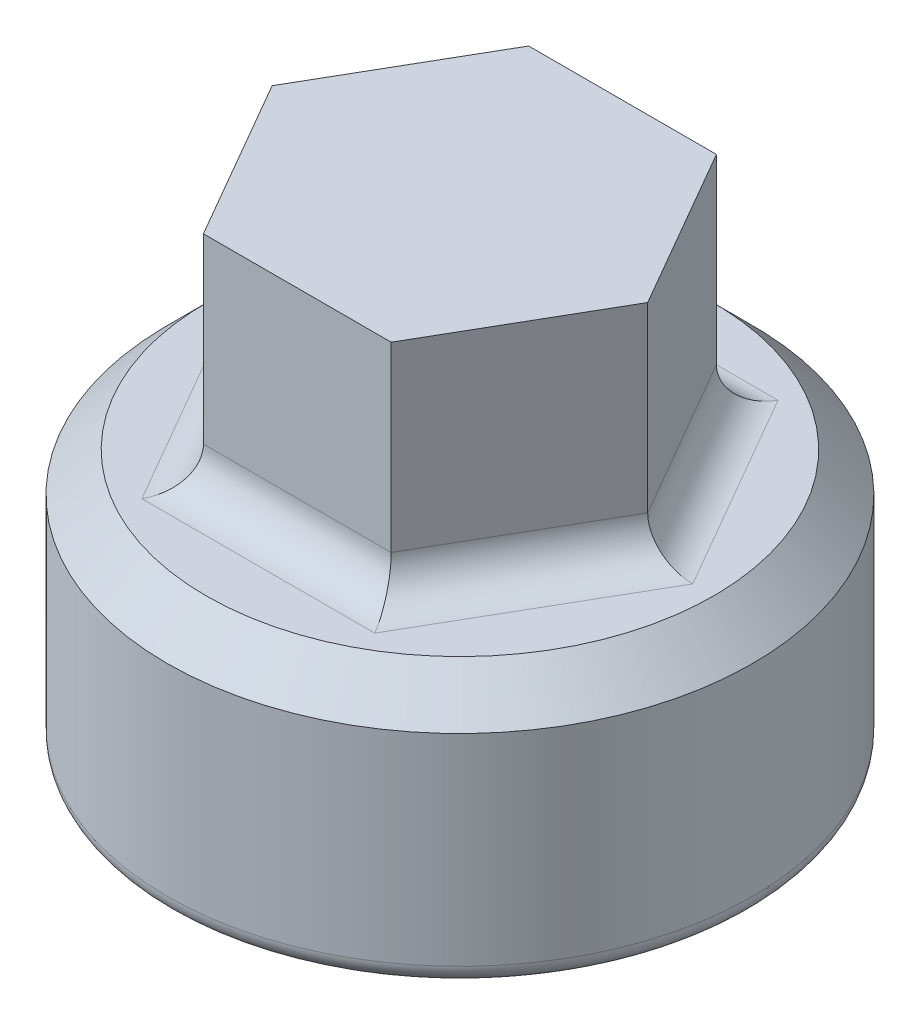
SolidWorks part; units mm, degrees
material "7050-T7651"
ref_plane "Front Plane" through (0, 0, 0) normal (0, 0, 1) x (1, 0, 0)
ref_plane "Top Plane" through (0, 0, 0) normal (0, 1, 0) x (1, 0, 0)
ref_plane "Right Plane" through (0, 0, 0) normal (1, 0, 0) x (0, 0, -1)
sketch "Sketch1" plane through (0, 0, 0) normal (0, 1, 0) x (1, 0, 0)
  line L1 (37.8164, 0) -> (18.9082, 32.75)
  line L2 (18.9082, 32.75) -> (-18.9082, 32.75)
  line L3 (-18.9082, 32.75) -> (-37.8164, 0)
  line L4 (-37.8164, 0) -> (-18.9082, -32.75)
  line L5 (-18.9082, -32.75) -> (18.9082, -32.75)
  line L6 (18.9082, -32.75) -> (37.8164, 0)
  circle A0 centre (0, 0) radius 45
  circle A1 centre (0, 0) radius 32.75 construction
  dimension "D2" = 90
  dimension "D1" = 65.5
extrude "Boss-Extrude1" add sketch "Sketch1" along normal blind 34
sketch "Sketch2" plane through (0, 34, 0) normal (0, 1, 0) x (1, 0, 0)
  circle A0 centre (0, 0) radius 45 construction
  circle A1 centre (0, 0) radius 45
extrude "Boss-Extrude2" add sketch "Sketch2" along normal blind 6
sketch "Sketch3" plane through (0, 40, 0) normal (0, 1, 0) x (1, 0, 0)
  line L1 (28.8675, 0) -> (14.4338, 25)
  line L2 (14.4338, 25) -> (-14.4338, 25)
  line L3 (-14.4338, 25) -> (-28.8675, 0)
  line L4 (-28.8675, 0) -> (-14.4338, -25)
  line L5 (-14.4338, -25) -> (14.4338, -25)
  line L6 (14.4338, -25) -> (28.8675, 0)
  circle A0 centre (0, 0) radius 25 construction
  dimension "D1" = 50
extrude "Boss-Extrude3" add sketch "Sketch3" along normal blind 34
fillet "Fillet1" radius 6 6 edges at (0, 40, 25) (21.6506, 40, 12.5) (21.6506, 40, -12.5) (-21.6506, 40, 12.5) (0, 40, -25) (-21.6506, 40, -12.5)
chamfer "Chamfer1" distance 6 angle 45 1 edges at (0, 40, 45)
fillet "Fillet2" radius 3 1 edges at (0, 0, 45)
fillet "Fillet3" radius 6.35 6 edges at (-18.9082, 17, -32.75) (18.9082, 17, -32.75) (37.8164, 17, 0) (18.9082, 17, 32.75) (-18.9082, 17, 32.75) (-37.8164, 17, 0)
sketch "Sketch4" plane through (0, 0, 0) normal (0, -1, 0) x (1, 0, 0)
  line L0 (0, 0) -> (18.417, 31.8993) construction
  line L1 (15.242, 32.75) -> (21.3374, 32.75) construction
  line L2 (20.7413, 29.575) -> (17.082, 35.9131) construction
  line L3 (20.7413, 29.575) -> (35.9834, 3.175) construction
  arc A0 (20.7413, 29.575) -> (15.242, 32.75) centre (15.242, 26.4) ccw construction
  circle A1 centre (17.3207, 30.0004) radius 3.175
  circle A2 centre (34.6414, 0) radius 3.175
  circle A3 centre (17.3207, -30.0004) radius 3.175
  circle A4 centre (-17.3207, -30.0004) radius 3.175
  circle A5 centre (-34.6414, 0) radius 3.175
  circle A6 centre (-17.3207, 30.0004) radius 3.175
  point P14 (18.9082, 32.75)
  point P29 (0, 0)
  dimension "D1" = 6.35
  dimension "D2" = 6
extrude "Cut-Extrude1" cut sketch "Sketch4" against normal up to surface (34 mm away) up to face at (0, 34, 0)
